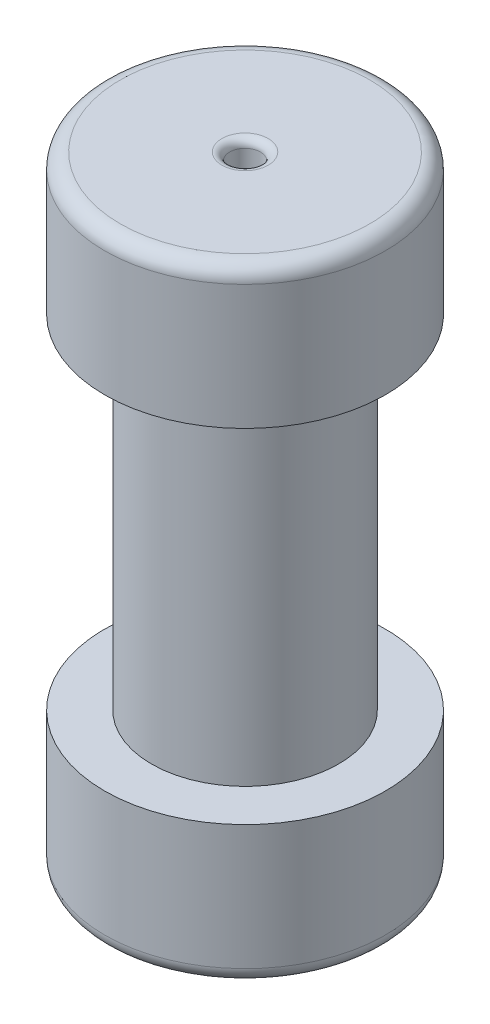
SolidWorks part; units mm, degrees
ref_plane "Front Plane" through (0, 0, 0) normal (0, 0, 1) x (1, 0, 0)
ref_plane "Top Plane" through (0, 0, 0) normal (0, 1, 0) x (1, 0, 0)
ref_plane "Right Plane" through (0, 0, 0) normal (1, 0, 0) x (0, 0, -1)
sketch "Sketch1" plane through (0, 0, 0) normal (0, 1, 0) x (1, 0, 0)
  circle A0 centre (0, 0) radius 22.86
  dimension "D1" = 45.72
extrude "Boss-Extrude1" add sketch "Sketch1" along normal blind 22.86
sketch "Sketch3" plane through (0, 22.86, 0) normal (0, 1, 0) x (1, 0, 0)
  circle A0 centre (0, 0) radius 15.24
  dimension "D1" = 30.48
extrude "Boss-Extrude2" add sketch "Sketch3" along normal blind 55.88
sketch "Sketch4" plane through (0, 78.74, 0) normal (0, 1, 0) x (1, 0, 0)
  circle A0 centre (0, 0) radius 22.86
  dimension "D1" = 45.72
extrude "Boss-Extrude3" add sketch "Sketch4" along normal blind 22.86
fillet "Fillet3" radius 2.54 2 edges at (0, 0, 22.86) (0, 101.6, 22.86)
sketch "Sketch5" plane through (0, 101.6, 0) normal (0, 1, 0) x (1, 0, 0)
  circle A0 centre (0, 0) radius 2.5
  dimension "D1" = 5
extrude "Cut-Extrude1" cut sketch "Sketch5" against normal blind 7
fillet "Fillet4" radius 1.27 1 edges at (0, 101.6, 2.5)
sketch "Sketch7" plane through (0, 101.6, 0) normal (0, 1, 0) x (1, 0, 0)
  circle A0 centre (0, 0) radius 10
  dimension "D1" = 20
sketch "Sketch8" plane through (0, 0, 0) normal (0, -1, 0) x (1, 0, 0)
  circle A0 centre (0, 0) radius 3.175
  dimension "D1" = 6.35
extrude "Boss-Extrude4" add sketch "Sketch8" along normal blind 12.7
